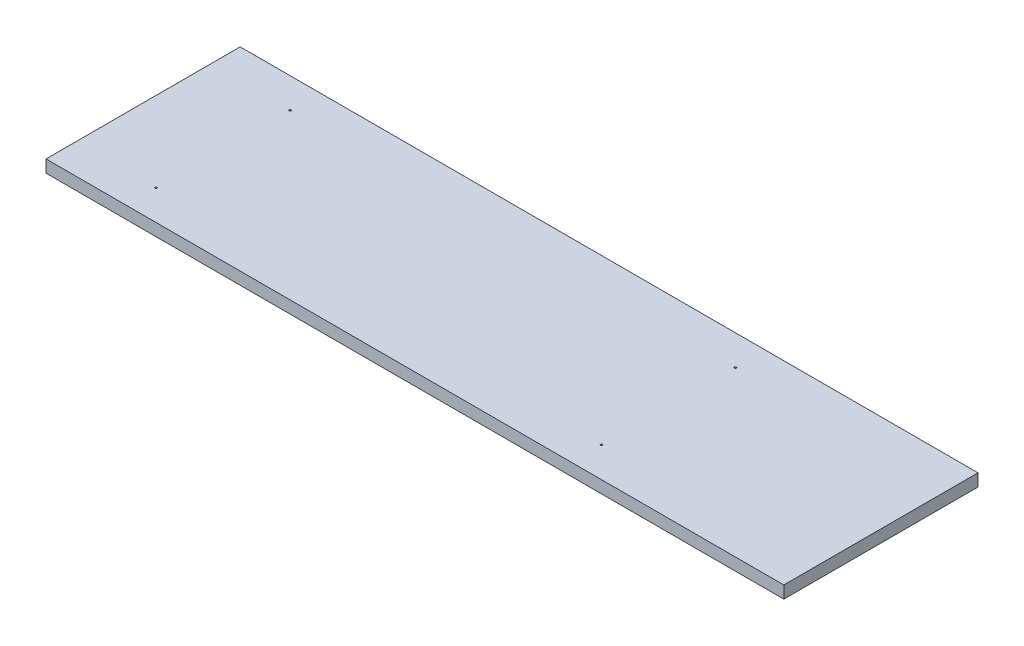
SolidWorks part; units mm, degrees
ref_plane "Front Plane" through (0, 0, 0) normal (0, 0, 1) x (1, 0, 0)
ref_plane "Top Plane" through (0, 0, 0) normal (0, 1, 0) x (1, 0, 0)
ref_plane "Right Plane" through (0, 0, 0) normal (1, 0, 0) x (0, 0, -1)
sketch "Sketch1" plane through (0, 0, 0) normal (0, 1, 0) x (1, 0, 0)
  line L1 (0, 0) -> (760, 0)
  line L2 (0, 0) -> (0, 200)
  line L3 (0, 200) -> (760, 200)
  line L4 (760, 0) -> (760, 200)
extrude "Boss-Extrude1" add sketch "Sketch1" against normal blind 12.7
sketch "Sketch2" plane through (0, 0, 0) normal (0, 1, 0) x (1, 0, 0)
  line L0 (0, 200) -> (0, 0) construction
  line L1 (0, 0) -> (760, 0) construction
  circle A0 centre (82.4, 31) radius 1
  circle A1 centre (82.4, 169) radius 1
  circle A2 centre (541.2, 31) radius 1
  circle A3 centre (541.2, 169) radius 1
  dimension "D1" = 138
  dimension "D2" = 458.8
  dimension "D3" = 82.4
  dimension "D4" = 31
extrude "Cut-Extrude1" cut sketch "Sketch2" against normal blind 8
